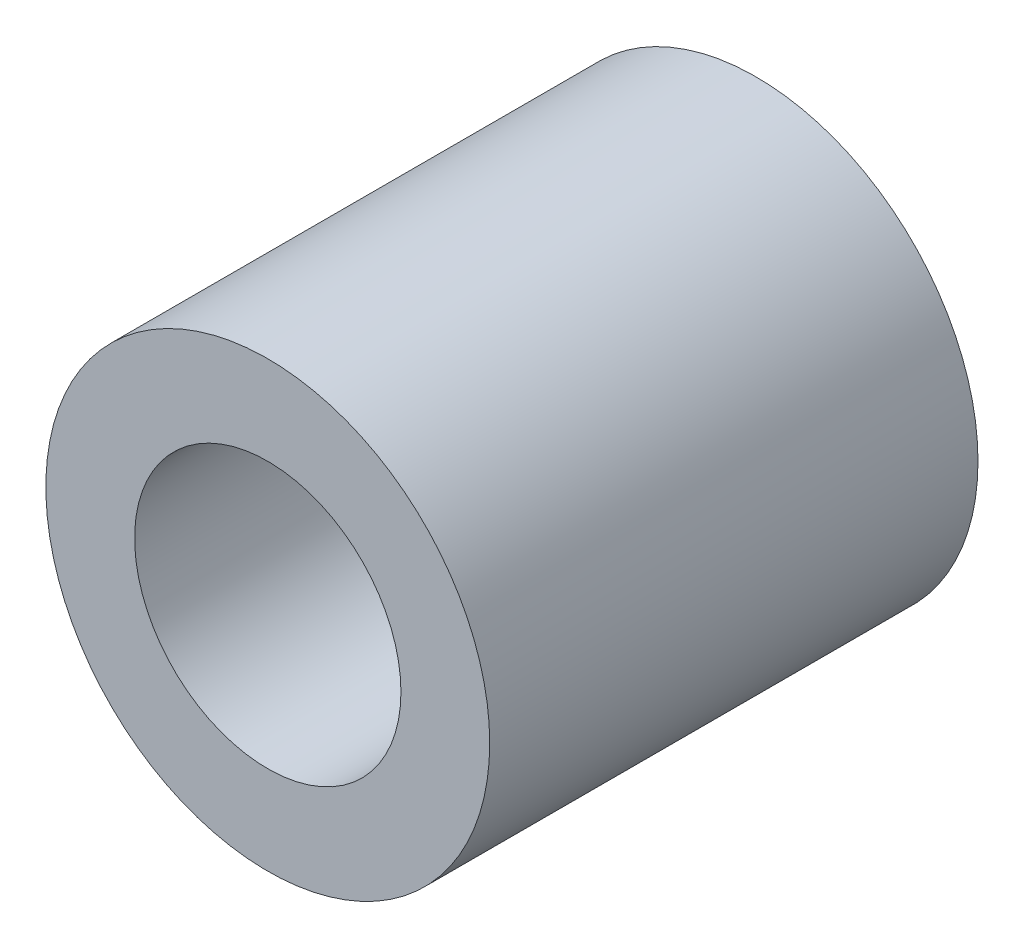
SolidWorks part; units mm, degrees
ref_plane "Plan de face" through (0, 0, 0) normal (0, 0, 1) x (1, 0, 0)
ref_plane "Plan de dessus" through (0, 0, 0) normal (0, 1, 0) x (1, 0, 0)
ref_plane "Plan de droite" through (0, 0, 0) normal (1, 0, 0) x (0, 0, -1)
sketch "Esquisse1" plane through (0, 0, 0) normal (0, 0, 1) x (1, 0, 0)
  circle A0 centre (0, 0) radius 15
  circle A1 centre (0, 0) radius 25
  dimension "D1" = 30
  dimension "D2" = 50
extrude "Boss.-Extru.1" add sketch "Esquisse1" along normal blind 55
